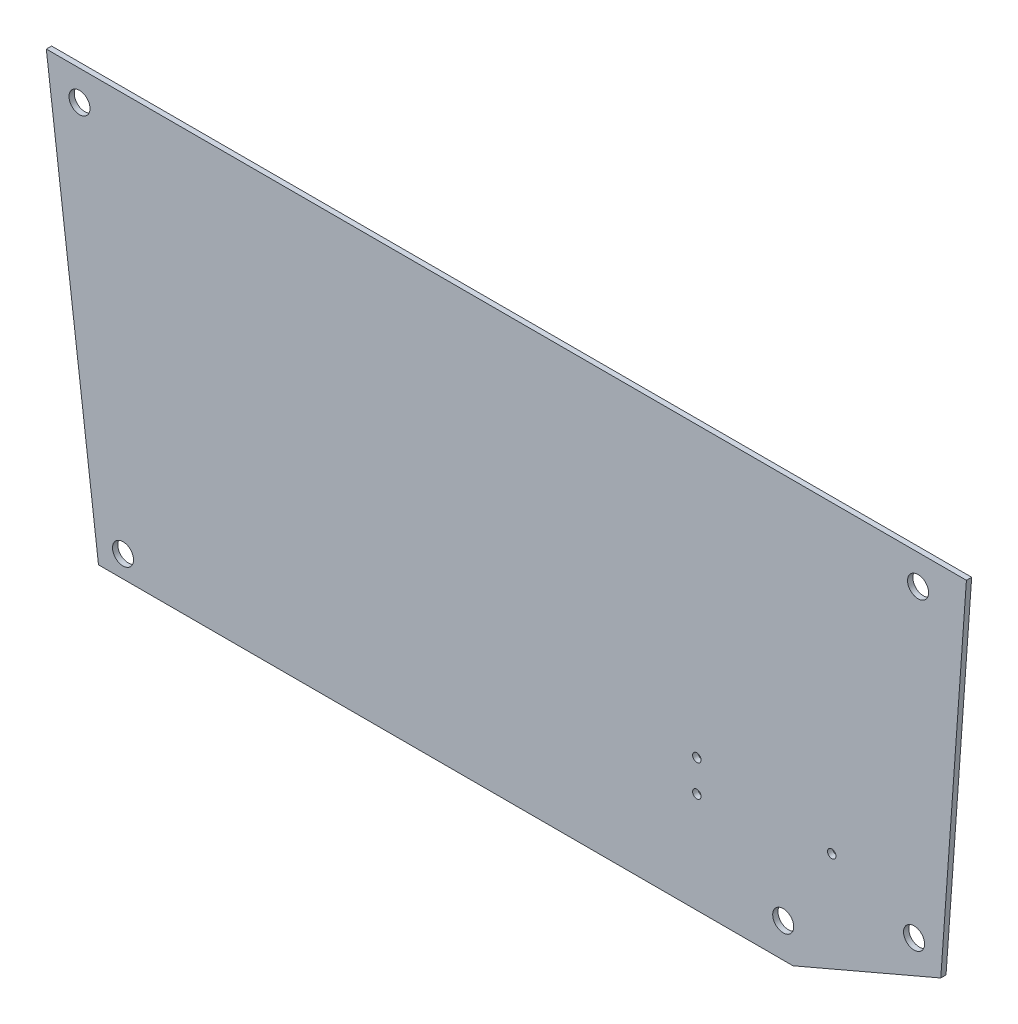
SolidWorks part; units mm, degrees
ref_plane "Front Plane" through (0, 0, 0) normal (0, 0, 1) x (1, 0, 0)
ref_plane "Top Plane" through (0, 0, 0) normal (0, 1, 0) x (1, 0, 0)
ref_plane "Right Plane" through (0, 0, 0) normal (1, 0, 0) x (0, 0, -1)
sketch "Sketch1" plane through (0, 0, 0) normal (0, 0, 1) x (1, 0, 0)
  line L0 (-58.4478, 2.2522) -> (205.7195, 2.2522)
  line L1 (169.1589, 52.5476) -> (169.1589, 40.5476) construction
  line L2 (205.7195, 2.2522) -> (261.9466, 26.3473)
  line L3 (261.9466, 26.3473) -> (271.7035, 162.2522)
  line L4 (271.7035, 162.2522) -> (-78.2965, 162.2522)
  line L5 (-78.2965, 162.2522) -> (-58.4478, 2.2522)
  line L9 (169.1589, 46.5476) -> (220.4571, 46.5476) construction
  circle A3 centre (169.1589, 40.5476) radius 1.6
  circle A4 centre (169.1589, 52.5476) radius 1.6
  circle A5 centre (220.4571, 46.5476) radius 1.6
  circle A6 centre (-65.6744, 150.9443) radius 4
  circle A7 centre (253.3111, 150.9443) radius 4
  circle A8 centre (251.7873, 34.4583) radius 4
  circle A9 centre (202.0128, 15.2522) radius 4
  circle A10 centre (-49.1265, 10.545) radius 4
  point P2 (169.1589, 46.5476)
  dimension "D4" = 8
  dimension "D1" = 12
  dimension "D2" = 350
  dimension "D3" = 160
  dimension "D5" = 13
  dimension "D6" = 13
  dimension "D7" = 51.2982
  dimension "D8" = 44.2954
extrude "Boss-Extrude1" add sketch "Sketch1" along normal mid plane 2
